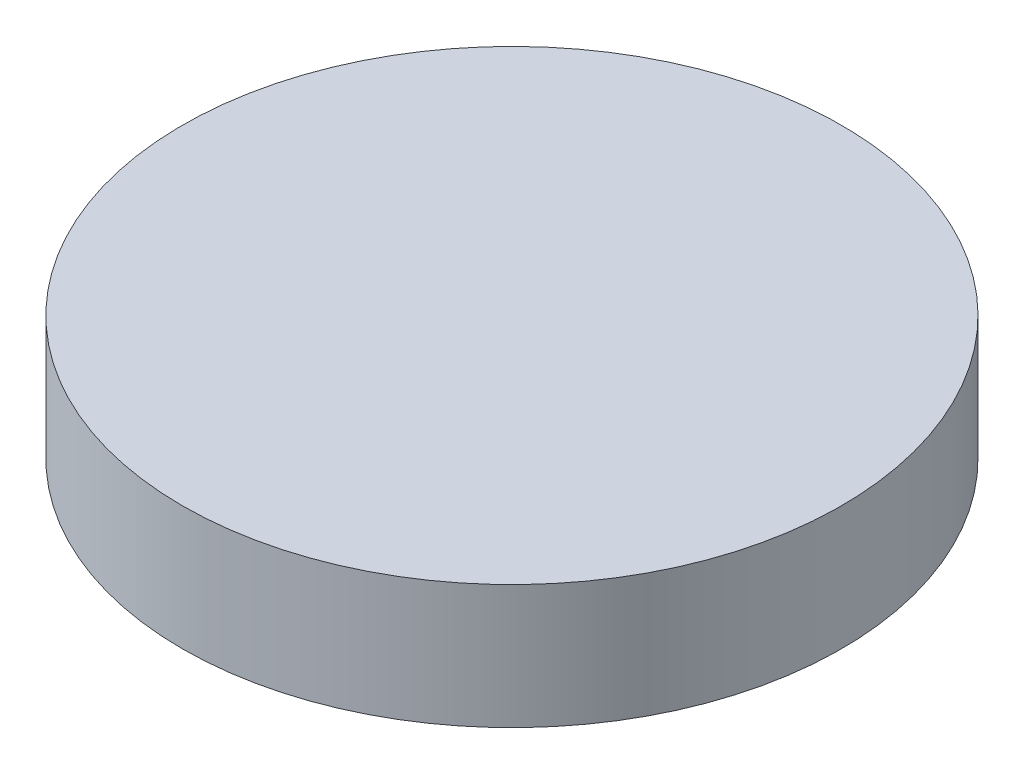
SolidWorks part; units mm, degrees
ref_plane "前视基准面" through (0, 0, 0) normal (0, 0, 1) x (1, 0, 0)
ref_plane "上视基准面" through (0, 0, 0) normal (0, 1, 0) x (1, 0, 0)
ref_plane "右视基准面" through (0, 0, 0) normal (1, 0, 0) x (0, 0, -1)
sketch "草图1" plane through (0, 0, 0) normal (0, 1, 0) x (1, 0, 0)
  circle A0 centre (0, 0) radius 50.8
  dimension "D1" = 101.6
extrude "凸台-拉伸1" add sketch "草图1" along normal blind 19.1
